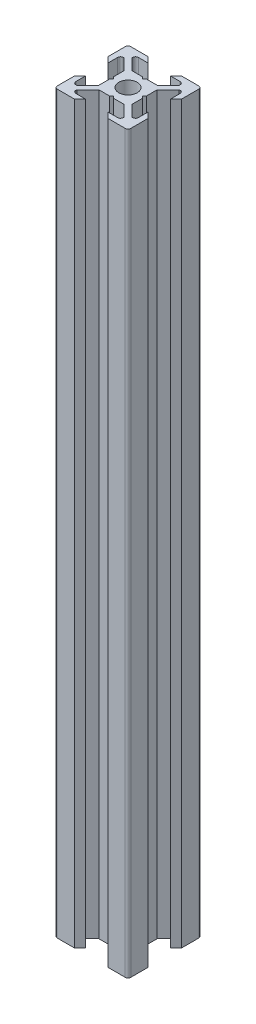
SolidWorks part; units mm, degrees
ref_plane "Face" through (0, 0, 0) normal (0, 0, 1) x (1, 0, 0)
ref_plane "Dessus" through (0, 0, 0) normal (0, 1, 0) x (1, 0, 0)
ref_plane "Droite" through (0, 0, 0) normal (1, 0, 0) x (0, 0, -1)
sketch "Esquisse1" plane through (0, 0, 0) normal (0, 1, 0) x (1, 0, 0)
  line L0 (0, 0) -> (0, 10) construction
  line L1 (0, 0) -> (-10, 0) construction
  line L2 (-10, 0) -> (-10, 10) construction
  line L3 (-10, 10) -> (0, 10) construction
  line L4 (0, 4) -> (-0.5, 4.5)
  line L5 (-0.5, 4.5) -> (-3.4393, 4.5)
  line L6 (-3.4393, 4.5) -> (-6.4393, 7.5)
  line L7 (-6.4393, 7.5) -> (-6.4393, 8.5)
  line L8 (-6.4393, 8.5) -> (-3, 8.5)
  line L9 (-3, 8.5) -> (-4.5, 10)
  line L10 (-4.5, 10) -> (-10, 10)
  line L11 (0, 0) -> (-10, 10) construction
  line L12 (-10, 4.5) -> (-10, 10)
  line L13 (-8.5, 3) -> (-10, 4.5)
  line L14 (-8.5, 6.4393) -> (-8.5, 3)
  line L15 (-7.5, 6.4393) -> (-8.5, 6.4393)
  line L16 (-4.5, 3.4393) -> (-7.5, 6.4393)
  line L17 (-4.5, 0.5) -> (-4.5, 3.4393)
  line L18 (-4, 0) -> (-4.5, 0.5)
  line L19 (0, -4) -> (-0.5, -4.5)
  line L20 (-0.5, -4.5) -> (-3.4393, -4.5)
  line L21 (-4, 0) -> (-4.5, -0.5)
  line L22 (-4.5, -0.5) -> (-4.5, -3.4393)
  line L23 (-4.5, -3.4393) -> (-7.5, -6.4393)
  line L24 (-3.4393, -4.5) -> (-6.4393, -7.5)
  line L25 (-3, -8.5) -> (-4.5, -10)
  line L26 (-6.4393, -8.5) -> (-3, -8.5)
  line L27 (-6.4393, -7.5) -> (-6.4393, -8.5)
  line L28 (-7.5, -6.4393) -> (-8.5, -6.4393)
  line L29 (-4.5, -10) -> (-10, -10)
  line L30 (-10, -4.5) -> (-10, -10)
  line L31 (-8.5, -3) -> (-10, -4.5)
  line L32 (-8.5, -6.4393) -> (-8.5, -3)
  line L33 (8.5, -6.4393) -> (8.5, -3)
  line L34 (8.5, -3) -> (10, -4.5)
  line L35 (10, -4.5) -> (10, -10)
  line L36 (4.5, -10) -> (10, -10)
  line L37 (7.5, -6.4393) -> (8.5, -6.4393)
  line L38 (6.4393, -7.5) -> (6.4393, -8.5)
  line L39 (6.4393, -8.5) -> (3, -8.5)
  line L40 (3, -8.5) -> (4.5, -10)
  line L41 (3.4393, -4.5) -> (6.4393, -7.5)
  line L42 (4.5, -3.4393) -> (7.5, -6.4393)
  line L43 (4.5, -0.5) -> (4.5, -3.4393)
  line L44 (4, 0) -> (4.5, -0.5)
  line L45 (0.5, -4.5) -> (3.4393, -4.5)
  line L46 (0, -4) -> (0.5, -4.5)
  line L47 (4, 0) -> (4.5, 0.5)
  line L48 (4.5, 0.5) -> (4.5, 3.4393)
  line L49 (4.5, 3.4393) -> (7.5, 6.4393)
  line L50 (7.5, 6.4393) -> (8.5, 6.4393)
  line L51 (8.5, 6.4393) -> (8.5, 3)
  line L52 (8.5, 3) -> (10, 4.5)
  line L53 (10, 4.5) -> (10, 10)
  line L54 (4.5, 10) -> (10, 10)
  line L55 (3, 8.5) -> (4.5, 10)
  line L56 (6.4393, 8.5) -> (3, 8.5)
  line L57 (6.4393, 7.5) -> (6.4393, 8.5)
  line L58 (3.4393, 4.5) -> (6.4393, 7.5)
  line L59 (0.5, 4.5) -> (3.4393, 4.5)
  line L60 (0, 4) -> (0.5, 4.5)
  circle A0 centre (0, 0) radius 2.5
  dimension "D10" = 5
  dimension "D1" = 10
  dimension "D2" = 45
  dimension "D3" = 45
  dimension "D4" = 1.5
  dimension "D5" = 7
  dimension "D6" = 1
  dimension "D7" = 4.5
  dimension "D8" = 0.5
  dimension "D9" = 0.75
extrude "Extrusion1" add sketch "Esquisse1" along normal blind 200
fillet "Congé1" radius 0.75 12 edges at (-8.5, 100, -6.4393) (-6.4393, 100, -8.5) (8.5, 100, -6.4393) (6.4393, 100, -8.5) (-8.5, 100, 6.4393) (-6.4393, 100, 8.5) (8.5, 100, 6.4393) (6.4393, 100, 8.5) (10, 100, -10) (-10, 100, -10) (-10, 100, 10) (10, 100, 10)
